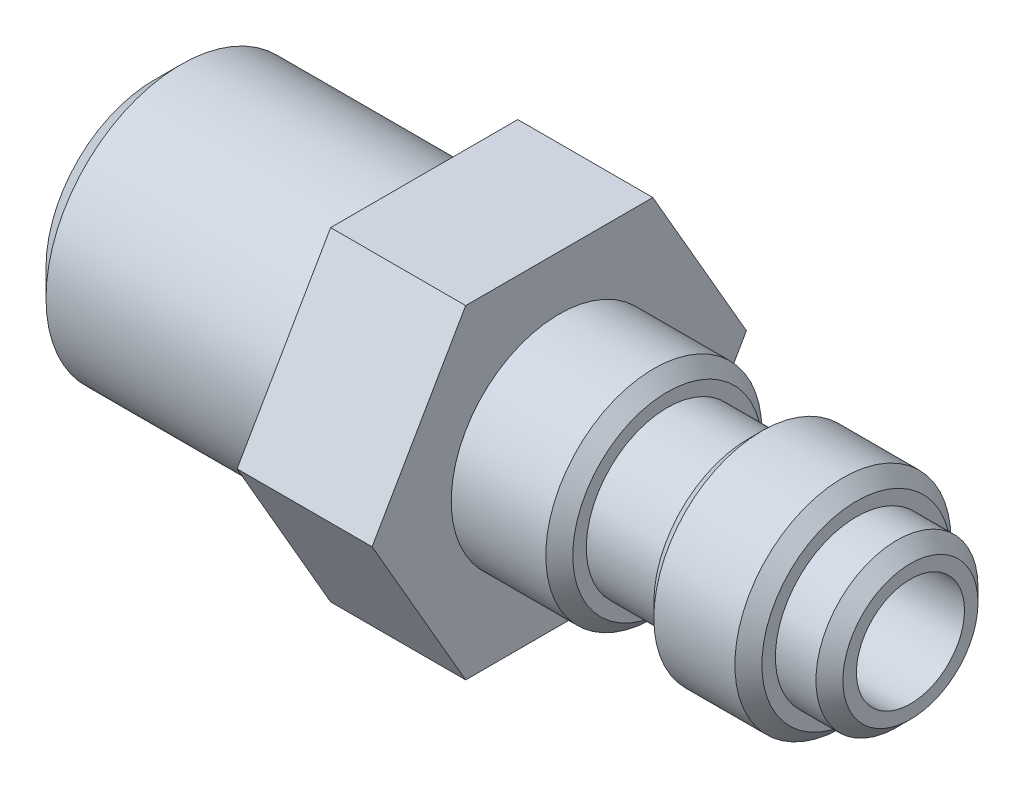
SolidWorks part; units mm, degrees
material "1.6523 (20NiCrMoS2-2)"
ref_plane "Front Plane" through (0, 0, 0) normal (0, 0, 1) x (1, 0, 0)
ref_plane "Top Plane" through (0, 0, 0) normal (0, 1, 0) x (1, 0, 0)
ref_plane "Right Plane" through (0, 0, 0) normal (1, 0, 0) x (0, 0, -1)
sketch "Sketch1" plane through (0, 0, 0) normal (0, 1, 0) x (1, 0, 0)
  line L0 (8.8798, 0) -> (-18.0437, 0) construction
  line L1 (0, 0) -> (0, 3)
  line L2 (0, 3) -> (-2, 3)
  line L3 (-2, 3) -> (-2, 4)
  line L4 (-2, 4) -> (-6, 4)
  line L5 (-6, 4) -> (-6, 3)
  line L6 (-6, 3) -> (-9, 3)
  line L7 (-9, 3) -> (-9, 4)
  line L8 (-9, 4) -> (-13, 4)
  line L9 (-13, 4) -> (-13, 0)
  line L10 (0, 0) -> (-13, 0)
  dimension "D1" = 13
  dimension "D2" = 8
  dimension "D3" = 3
  dimension "D4" = 2
  dimension "D5" = 4
  dimension "D6" = 1
revolve "Revolve1" add sketch "Sketch1" angle 360 about L0
sketch "Sketch2" plane through (-13, 0, 0) normal (-1, 0, 0) x (0, 0, 1)
  line L1 (6.9282, 0) -> (3.4641, 6)
  line L2 (3.4641, 6) -> (-3.4641, 6)
  line L3 (-3.4641, 6) -> (-6.9282, 0)
  line L4 (-6.9282, 0) -> (-3.4641, -6)
  line L5 (-3.4641, -6) -> (3.4641, -6)
  line L6 (3.4641, -6) -> (6.9282, 0)
  circle A0 centre (0, 0) radius 6 construction
  dimension "D1" = 12
extrude "Boss-Extrude1" add sketch "Sketch2" along normal blind 5
sketch "Sketch3" plane through (-18, 0, 0) normal (-1, 0, 0) x (0, 0, 1)
  circle A0 centre (0, 0) radius 5
  dimension "D1" = 10
extrude "Boss-Extrude2" add sketch "Sketch3" along normal blind 10
sketch "Sketch4" plane through (0, 0, 0) normal (1, 0, 0) x (0, 0, -1)
  circle A0 centre (0, 0) radius 2
  dimension "D1" = 4
extrude "Cut-Extrude1" cut sketch "Sketch4" against normal through all
chamfer "Chamfer1" distance 0.5 angle 45 5 edges at (0, 0, -3) (-2, 0, -4) (-6, 0, -4) (-9, 0, -4) (-28, 0, -2)
chamfer "Chamfer2" distance 1 angle 45 1 edges at (-28, 0, 5)
